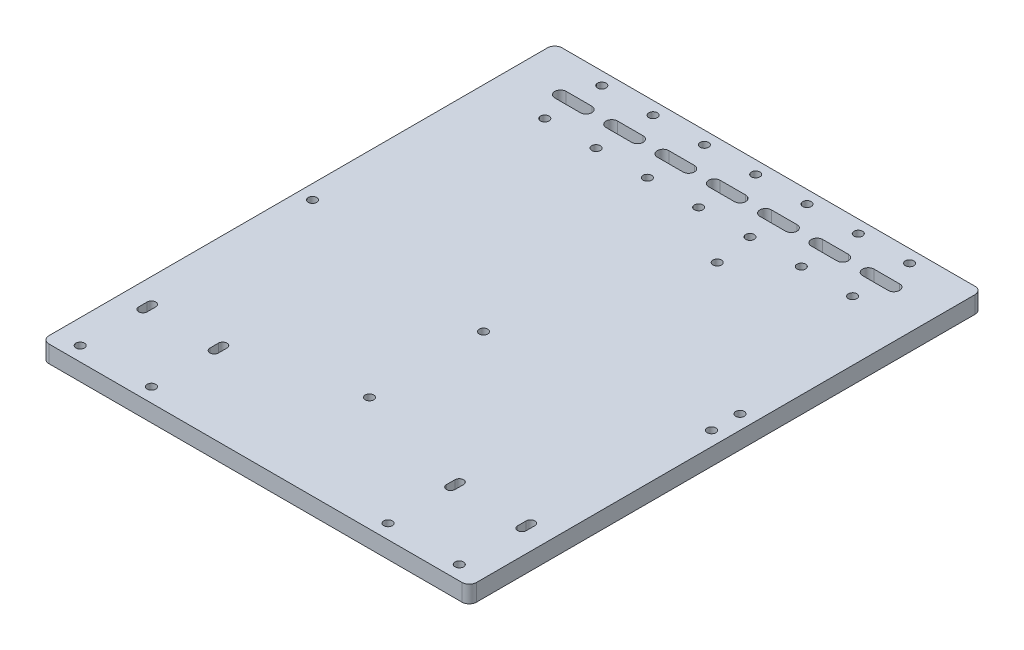
SolidWorks part; units mm, degrees
ref_plane "Front Plane" through (0, 0, 0) normal (0, 0, 1) x (1, 0, 0)
ref_plane "Top Plane" through (0, 0, 0) normal (0, 1, 0) x (1, 0, 0)
ref_plane "Right Plane" through (0, 0, 0) normal (1, 0, 0) x (0, 0, -1)
sketch "Sketch1" plane through (0, 0, 0) normal (0, 1, 0) x (1, 0, 0)
  line L0 (75, 180) -> (75, 0) construction
  line L1 (2.54, 0) -> (147.46, 0)
  line L2 (0, 2.54) -> (0, 177.46)
  line L3 (2.54, 180) -> (147.46, 180)
  line L4 (150, 2.54) -> (150, 177.46)
  line L5 (133.5, 165.5) -> (124.5, 165.5) construction
  line L6 (80, 142) -> (80, 92) construction
  line L7 (133.5, 167.5) -> (124.5, 167.5)
  line L8 (16.5, 165.5) -> (25.5, 165.5) construction
  line L9 (16.5, 167.5) -> (25.5, 167.5)
  line L10 (16.5, 163.5) -> (25.5, 163.5)
  line L11 (34.5, 165.5) -> (43.5, 165.5) construction
  line L12 (34.5, 167.5) -> (43.5, 167.5)
  line L13 (34.5, 163.5) -> (43.5, 163.5)
  line L14 (52.5, 165.5) -> (61.5, 165.5) construction
  line L15 (52.5, 167.5) -> (61.5, 167.5)
  line L16 (52.5, 163.5) -> (61.5, 163.5)
  line L17 (70.5, 165.5) -> (79.5, 165.5) construction
  line L18 (70.5, 167.5) -> (79.5, 167.5)
  line L19 (70.5, 163.5) -> (79.5, 163.5)
  line L20 (133.5, 163.5) -> (124.5, 163.5)
  line L21 (115.5, 165.5) -> (106.5, 165.5) construction
  line L22 (115.5, 167.5) -> (106.5, 167.5)
  line L23 (115.5, 163.5) -> (106.5, 163.5)
  line L24 (97.5, 165.5) -> (88.5, 165.5) construction
  line L25 (97.5, 167.5) -> (88.5, 167.5)
  line L26 (97.5, 163.5) -> (88.5, 163.5)
  line L27 (80, 92) -> (0, 92) construction
  line L28 (0, 142) -> (0, 92) construction
  line L29 (0, 142) -> (80, 142) construction
  line L30 (8.5006, 30) -> (8.5006, 27) construction
  line L31 (10.0006, 30) -> (10.0006, 27)
  line L32 (33.5006, 30) -> (33.5006, 27) construction
  line L33 (35.0006, 30) -> (35.0006, 27)
  line L34 (32.0006, 30) -> (32.0006, 27)
  line L35 (7.0006, 30) -> (7.0006, 27)
  line L36 (116.4994, 30) -> (116.4994, 27) construction
  line L37 (114.9994, 30) -> (114.9994, 27)
  line L38 (117.9994, 30) -> (117.9994, 27)
  line L39 (141.4994, 30) -> (141.4994, 27) construction
  line L40 (139.9994, 30) -> (139.9994, 27)
  line L41 (142.9994, 30) -> (142.9994, 27)
  arc A0 (150, 177.46) -> (147.46, 180) centre (147.46, 177.46) ccw
  arc A1 (147.46, 0) -> (150, 2.54) centre (147.46, 2.54) ccw
  arc A2 (2.54, 0) -> (0, 2.54) centre (2.54, 2.54) cw
  arc A3 (2.54, 180) -> (0, 177.46) centre (2.54, 177.46) ccw
  circle A6 centre (33.5006, 5) radius 1.5
  circle A7 centre (8.5006, 5) radius 1.5
  circle A8 centre (141.4994, 5) radius 1.5
  circle A9 centre (116.4994, 5) radius 1.5
  circle A12 centre (75, 155.5) radius 1.5
  circle A13 centre (39, 155.5) radius 1.5
  circle A14 centre (21, 155.5) radius 1.5
  circle A15 centre (57, 155.5) radius 1.5
  circle A16 centre (93, 155.5) radius 1.5
  circle A17 centre (111, 155.5) radius 1.5
  circle A18 centre (129, 155.5) radius 1.5
  circle A26 centre (129, 175.5) radius 1.5
  circle A27 centre (111, 175.5) radius 1.5
  circle A28 centre (93, 175.5) radius 1.5
  circle A29 centre (75, 175.5) radius 1.5
  circle A30 centre (57, 175.5) radius 1.5
  circle A31 centre (39, 175.5) radius 1.5
  circle A32 centre (21, 175.5) radius 1.5
  circle A51 centre (145, 100) radius 1.5
  circle A52 centre (95, 142) radius 1.5
  arc A53 (16.5, 167.5) -> (16.5, 163.5) centre (16.5, 165.5) ccw
  arc A54 (25.5, 163.5) -> (25.5, 167.5) centre (25.5, 165.5) ccw
  arc A55 (34.5, 167.5) -> (34.5, 163.5) centre (34.5, 165.5) ccw
  arc A56 (43.5, 163.5) -> (43.5, 167.5) centre (43.5, 165.5) ccw
  arc A57 (52.5, 167.5) -> (52.5, 163.5) centre (52.5, 165.5) ccw
  arc A58 (61.5, 163.5) -> (61.5, 167.5) centre (61.5, 165.5) ccw
  arc A59 (70.5, 167.5) -> (70.5, 163.5) centre (70.5, 165.5) ccw
  arc A60 (79.5, 163.5) -> (79.5, 167.5) centre (79.5, 165.5) ccw
  arc A61 (133.5, 167.5) -> (133.5, 163.5) centre (133.5, 165.5) cw
  arc A62 (124.5, 163.5) -> (124.5, 167.5) centre (124.5, 165.5) cw
  arc A63 (115.5, 167.5) -> (115.5, 163.5) centre (115.5, 165.5) cw
  arc A64 (106.5, 163.5) -> (106.5, 167.5) centre (106.5, 165.5) cw
  arc A65 (97.5, 167.5) -> (97.5, 163.5) centre (97.5, 165.5) cw
  arc A66 (88.5, 163.5) -> (88.5, 167.5) centre (88.5, 165.5) cw
  circle A67 centre (145, 90) radius 1.5
  circle A68 centre (5, 90) radius 1.5
  circle A69 centre (75, 80) radius 1.5
  circle A70 centre (75, 40) radius 1.5
  arc A73 (35.0006, 30) -> (32.0006, 30) centre (33.5006, 30) ccw
  arc A74 (32.0006, 27) -> (35.0006, 27) centre (33.5006, 27) ccw
  arc A75 (10.0006, 30) -> (7.0006, 30) centre (8.5006, 30) ccw
  arc A76 (7.0006, 27) -> (10.0006, 27) centre (8.5006, 27) ccw
  arc A77 (114.9994, 30) -> (117.9994, 30) centre (116.4994, 30) cw
  arc A78 (117.9994, 27) -> (114.9994, 27) centre (116.4994, 27) cw
  arc A79 (139.9994, 30) -> (142.9994, 30) centre (141.4994, 30) cw
  arc A80 (142.9994, 27) -> (139.9994, 27) centre (141.4994, 27) cw
  point P11 (0, 0)
  point P17 (8.5006, 28.5)
  point P30 (116.4994, 28.5)
  point P50 (21, 165.5)
  point P56 (39, 165.5)
  point P81 (57, 165.5)
  point P88 (75, 165.5)
  point P101 (129, 165.5)
  point P108 (111, 165.5)
  point P123 (93, 165.5)
  point P129 (0, 0)
  point P130 (0, 0)
  point P133 (33.5006, 28.5)
  point P142 (141.4994, 28.5)
  dimension "D1" = 2.54
  dimension "D4" = 3
  dimension "D9" = 3
  dimension "D10" = 18
  dimension "D11" = 18
  dimension "D12" = 18
  dimension "D13" = 9
  dimension "D18" = 180
  dimension "D19" = 100
  dimension "D20" = 3
  dimension "D21" = 5
  dimension "D22" = 5
  dimension "D23" = 3
  dimension "D24" = 90
  dimension "D25" = 3
  dimension "D26" = 50
  dimension "D27" = 42
  dimension "D30" = 3
  dimension "D15" = 10
  dimension "D32" = 3
  dimension "D33" = 3
  dimension "D34" = 40
  dimension "D35" = 10
  dimension "D38" = 3
  dimension "D3" = 150
  dimension "D5" = 3
  dimension "D6" = 25
  dimension "D7" = 22
  dimension "D8" = 5
  dimension "D14" = 10
  dimension "D16" = 4.5
  dimension "D17" = 4
  dimension "D28" = 80
  dimension "D29" = 50
  dimension "D31" = 0
  dimension "D39" = 3
extrude "Boss-Extrude1" add sketch "Sketch1" along normal blind 6
